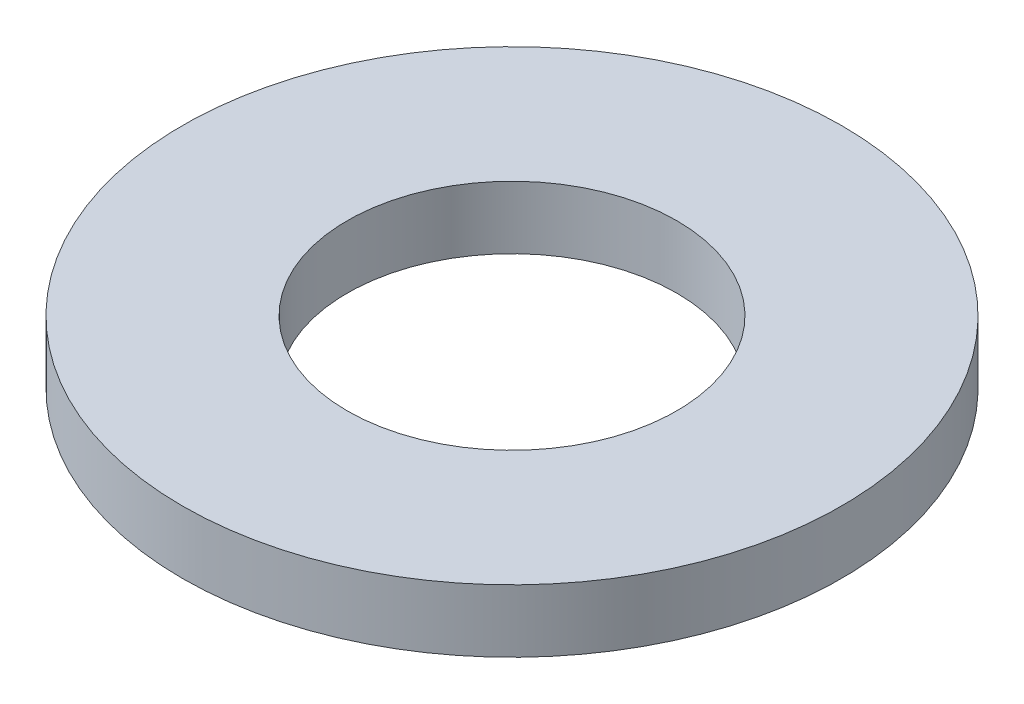
SolidWorks part; units mm, degrees
ref_plane "Płaszczyzna XY" through (0, 0, 0) normal (0, 0, 1) x (1, 0, 0)
ref_plane "Płaszczyzna XZ" through (0, 0, 0) normal (0, 1, 0) x (1, 0, 0)
ref_plane "Płaszczyzna YZ" through (0, 0, 0) normal (1, 0, 0) x (0, 0, -1)
sketch "Szkic1" plane through (0, 0, 0) normal (0, 1, 0) x (1, 0, 0)
  circle A0 centre (0, 0) radius 10.5
  circle A1 centre (0, 0) radius 5.25
  dimension "D1" = 21
  dimension "D2" = 10.5
extrude "Dodanie-wyciągnięcie1" add sketch "Szkic1" along normal blind 2
